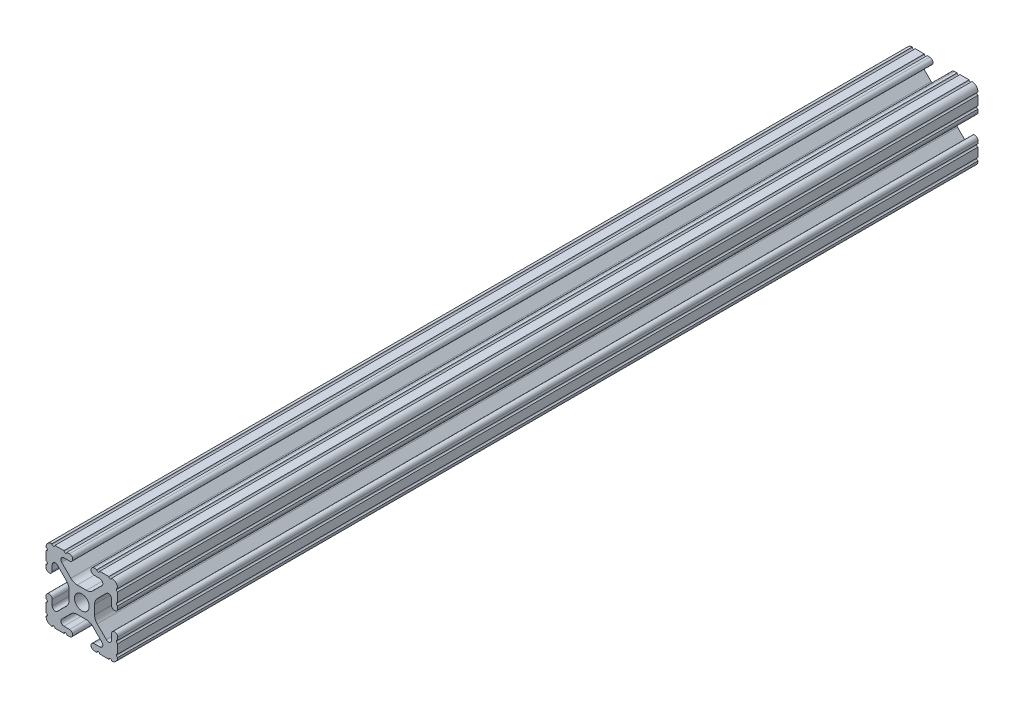
SolidWorks part; units mm, degrees
ref_plane "Front Plane" through (0, 0, 0) normal (0, 0, 1) x (1, 0, 0)
ref_plane "Top Plane" through (0, 0, 0) normal (0, 1, 0) x (1, 0, 0)
ref_plane "Right Plane" through (0, 0, 0) normal (1, 0, 0) x (0, 0, -1)
sketch "Sketch1" plane through (0, 0, 0) normal (1, 0, 0) x (0, 0, -1)
  line L0 (-152.4, 0) -> (152.4, 0)
  point P2 (0, 0)
  dimension "D1" = 304.8
other "Fractional 1010(1)"
ref_plane "Plane1" through (0, 0, 152.4) normal (0, 0, -1) x (0, 1, 0)
sketch "Sketch11" plane through (0, 0, 152.4) normal (0, 0, -1) x (0, 1, 0)
  line L0 (10.5918, 12.7) -> (10.5664, 12.7)
  line L1 (9.5504, 12.7) -> (6.3246, 12.7)
  line L2 (5.3086, 12.7) -> (4.3561, 12.7)
  line L3 (4.3561, 10.4902) -> (6.3701, 10.4902)
  line L4 (7.1192, 8.6817) -> (3.8846, 5.4471)
  line L5 (1.6396, 4.5172) -> (-1.6396, 4.5172)
  line L6 (-3.8846, 5.4471) -> (-7.1192, 8.6817)
  line L7 (-6.3701, 10.4902) -> (-4.3561, 10.4902)
  line L8 (-4.3561, 12.7) -> (-5.3086, 12.7)
  line L9 (-6.3246, 12.7) -> (-9.5504, 12.7)
  line L10 (-10.5664, 12.7) -> (-10.5918, 12.7)
  line L11 (-12.7, 10.5918) -> (-12.7, 10.5664)
  line L12 (-12.7, 9.5504) -> (-12.7, 6.3246)
  line L13 (-12.7, 5.3086) -> (-12.7, 4.3561)
  line L14 (-10.4902, 4.3561) -> (-10.4902, 6.3701)
  line L15 (-8.6817, 7.1192) -> (-5.4471, 3.8846)
  line L16 (-4.5172, 1.6396) -> (-4.5172, -1.6396)
  line L17 (-5.4471, -3.8846) -> (-8.6817, -7.1192)
  line L18 (-10.4902, -6.3701) -> (-10.4902, -4.3561)
  line L19 (-12.7, -4.3561) -> (-12.7, -5.3086)
  line L20 (-12.7, -6.3246) -> (-12.7, -9.5504)
  line L21 (-12.7, -10.5664) -> (-12.7, -10.5918)
  line L22 (-10.5918, -12.7) -> (-10.5664, -12.7)
  line L23 (-9.5504, -12.7) -> (-6.3246, -12.7)
  line L24 (-5.3086, -12.7) -> (-4.3561, -12.7)
  line L25 (-4.3561, -10.4902) -> (-6.3701, -10.4902)
  line L26 (-7.1192, -8.6817) -> (-3.8846, -5.4471)
  line L27 (-1.6396, -4.5172) -> (1.6396, -4.5172)
  line L28 (3.8846, -5.4471) -> (7.1192, -8.6817)
  line L29 (6.3701, -10.4902) -> (4.3561, -10.4902)
  line L30 (4.3561, -12.7) -> (5.3086, -12.7)
  line L31 (6.3246, -12.7) -> (9.5504, -12.7)
  line L32 (10.5664, -12.7) -> (10.5918, -12.7)
  line L33 (12.7, -10.5918) -> (12.7, -10.5664)
  line L34 (12.7, -9.5504) -> (12.7, -6.3246)
  line L35 (12.7, -5.3086) -> (12.7, -4.3561)
  line L36 (10.4902, -4.3561) -> (10.4902, -6.3701)
  line L37 (8.6817, -7.1192) -> (5.4471, -3.8846)
  line L38 (4.5172, -1.6396) -> (4.5172, 1.6396)
  line L39 (5.4471, 3.8846) -> (8.6817, 7.1192)
  line L40 (10.4902, 6.3701) -> (10.4902, 4.3561)
  line L41 (12.7, 4.3561) -> (12.7, 5.3086)
  line L42 (12.7, 6.3246) -> (12.7, 9.5504)
  line L43 (12.7, 10.5664) -> (12.7, 10.5918)
  circle A0 centre (0, 0) radius 2.6035
  arc A1 (12.7, 10.5918) -> (10.5918, 12.7) centre (10.5918, 10.5918) ccw
  arc A2 (9.5504, 12.7) -> (10.5664, 12.7) centre (10.0584, 12.7) ccw
  arc A3 (5.3086, 12.7) -> (6.3246, 12.7) centre (5.8166, 12.7) ccw
  arc A4 (4.3561, 12.7) -> (4.3561, 10.4902) centre (4.3561, 11.5951) ccw
  arc A5 (7.1192, 8.6817) -> (6.3701, 10.4902) centre (6.3701, 9.4308) ccw
  arc A6 (1.6396, 4.5172) -> (3.8846, 5.4471) centre (1.6396, 7.6922) ccw
  arc A7 (-3.8846, 5.4471) -> (-1.6396, 4.5172) centre (-1.6396, 7.6922) ccw
  arc A8 (-6.3701, 10.4902) -> (-7.1192, 8.6817) centre (-6.3701, 9.4308) ccw
  arc A9 (-4.3561, 10.4902) -> (-4.3561, 12.7) centre (-4.3561, 11.5951) ccw
  arc A10 (-6.3246, 12.7) -> (-5.3086, 12.7) centre (-5.8166, 12.7) ccw
  arc A11 (-10.5664, 12.7) -> (-9.5504, 12.7) centre (-10.0584, 12.7) ccw
  arc A12 (-10.5918, 12.7) -> (-12.7, 10.5918) centre (-10.5918, 10.5918) ccw
  arc A13 (-12.7, 9.5504) -> (-12.7, 10.5664) centre (-12.7, 10.0584) ccw
  arc A14 (-12.7, 5.3086) -> (-12.7, 6.3246) centre (-12.7, 5.8166) ccw
  arc A15 (-12.7, 4.3561) -> (-10.4902, 4.3561) centre (-11.5951, 4.3561) ccw
  arc A16 (-8.6817, 7.1192) -> (-10.4902, 6.3701) centre (-9.4308, 6.3701) ccw
  arc A17 (-4.5172, 1.6396) -> (-5.4471, 3.8846) centre (-7.6922, 1.6396) ccw
  arc A18 (-5.4471, -3.8846) -> (-4.5172, -1.6396) centre (-7.6922, -1.6396) ccw
  arc A19 (-10.4902, -6.3701) -> (-8.6817, -7.1192) centre (-9.4308, -6.3701) ccw
  arc A20 (-10.4902, -4.3561) -> (-12.7, -4.3561) centre (-11.5951, -4.3561) ccw
  arc A21 (-12.7, -6.3246) -> (-12.7, -5.3086) centre (-12.7, -5.8166) ccw
  arc A22 (-12.7, -10.5664) -> (-12.7, -9.5504) centre (-12.7, -10.0584) ccw
  arc A23 (-12.7, -10.5918) -> (-10.5918, -12.7) centre (-10.5918, -10.5918) ccw
  arc A24 (-9.5504, -12.7) -> (-10.5664, -12.7) centre (-10.0584, -12.7) ccw
  arc A25 (-5.3086, -12.7) -> (-6.3246, -12.7) centre (-5.8166, -12.7) ccw
  arc A26 (-4.3561, -12.7) -> (-4.3561, -10.4902) centre (-4.3561, -11.5951) ccw
  arc A27 (-7.1192, -8.6817) -> (-6.3701, -10.4902) centre (-6.3701, -9.4308) ccw
  arc A28 (-1.6396, -4.5172) -> (-3.8846, -5.4471) centre (-1.6396, -7.6922) ccw
  arc A29 (3.8846, -5.4471) -> (1.6396, -4.5172) centre (1.6396, -7.6922) ccw
  arc A30 (6.3701, -10.4902) -> (7.1192, -8.6817) centre (6.3701, -9.4308) ccw
  arc A31 (4.3561, -10.4902) -> (4.3561, -12.7) centre (4.3561, -11.5951) ccw
  arc A32 (6.3246, -12.7) -> (5.3086, -12.7) centre (5.8166, -12.7) ccw
  arc A33 (10.5664, -12.7) -> (9.5504, -12.7) centre (10.0584, -12.7) ccw
  arc A34 (10.5918, -12.7) -> (12.7, -10.5918) centre (10.5918, -10.5918) ccw
  arc A35 (12.7, -9.5504) -> (12.7, -10.5664) centre (12.7, -10.0584) ccw
  arc A36 (12.7, -5.3086) -> (12.7, -6.3246) centre (12.7, -5.8166) ccw
  arc A37 (12.7, -4.3561) -> (10.4902, -4.3561) centre (11.5951, -4.3561) ccw
  arc A38 (8.6817, -7.1192) -> (10.4902, -6.3701) centre (9.4308, -6.3701) ccw
  arc A39 (4.5172, -1.6396) -> (5.4471, -3.8846) centre (7.6922, -1.6396) ccw
  arc A40 (5.4471, 3.8846) -> (4.5172, 1.6396) centre (7.6922, 1.6396) ccw
  arc A41 (10.4902, 6.3701) -> (8.6817, 7.1192) centre (9.4308, 6.3701) ccw
  arc A42 (10.4902, 4.3561) -> (12.7, 4.3561) centre (11.5951, 4.3561) ccw
  arc A43 (12.7, 6.3246) -> (12.7, 5.3086) centre (12.7, 5.8166) ccw
  arc A44 (12.7, 10.5664) -> (12.7, 9.5504) centre (12.7, 10.0584) ccw
  point P0 (0, 0)
